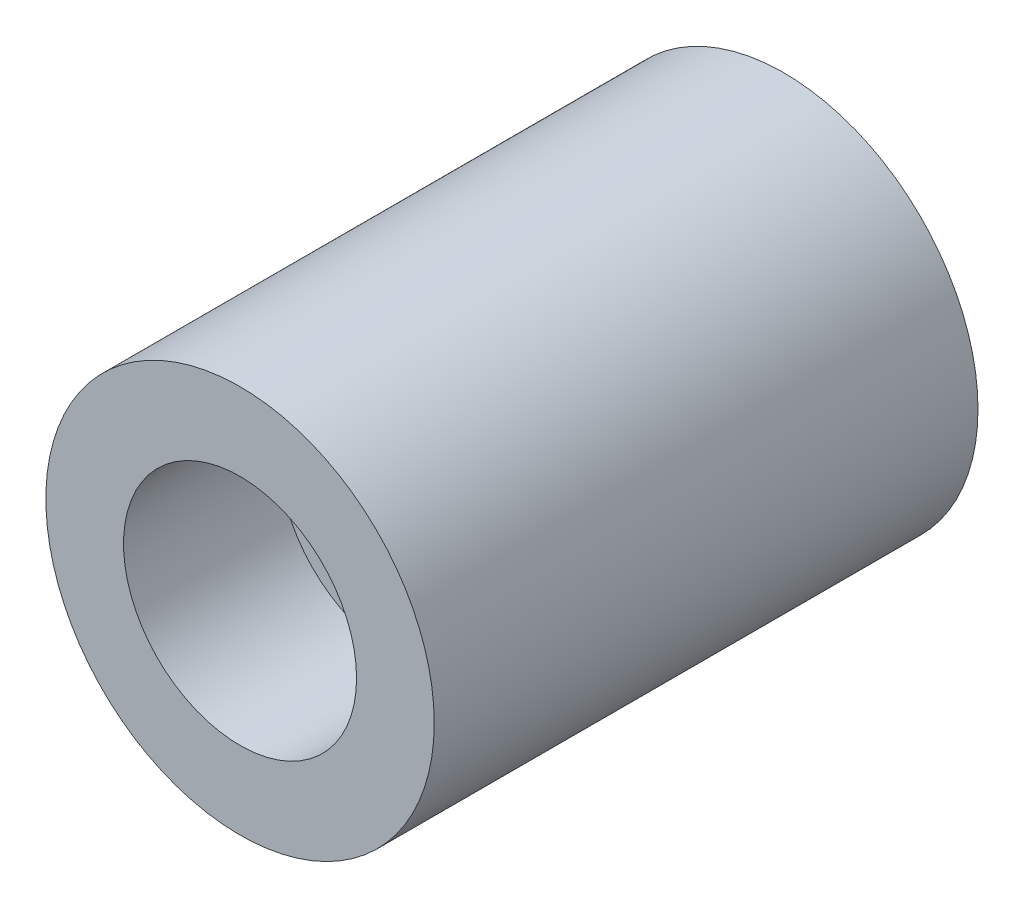
SolidWorks part; units mm, degrees
ref_plane "Front Plane" through (0, 0, 0) normal (0, 0, 1) x (1, 0, 0)
ref_plane "Top Plane" through (0, 0, 0) normal (0, 1, 0) x (1, 0, 0)
ref_plane "Right Plane" through (0, 0, 0) normal (1, 0, 0) x (0, 0, -1)
sketch "Sketch1" plane through (0, 0, 0) normal (0, 0, 1) x (1, 0, 0)
  circle A0 centre (0, 0) radius 50
  dimension "D1" = 50
extrude "Boss-Extrude1" add sketch "Sketch1" along normal blind 140
sketch "Sketch2" plane through (0, 0, 140) normal (0, 0, 1) x (1, 0, 0)
  circle A1 centre (0, 0) radius 10
  dimension "D2" = 10
extrude "Cut-Extrude1" cut sketch "Sketch2" against normal blind 120
sketch "Sketch3" plane through (0, 0, 140) normal (0, 0, 1) x (1, 0, 0)
  circle A0 centre (0, 0) radius 30
  dimension "D1" = 30
extrude "Cut-Extrude2" cut sketch "Sketch3" against normal blind 40
